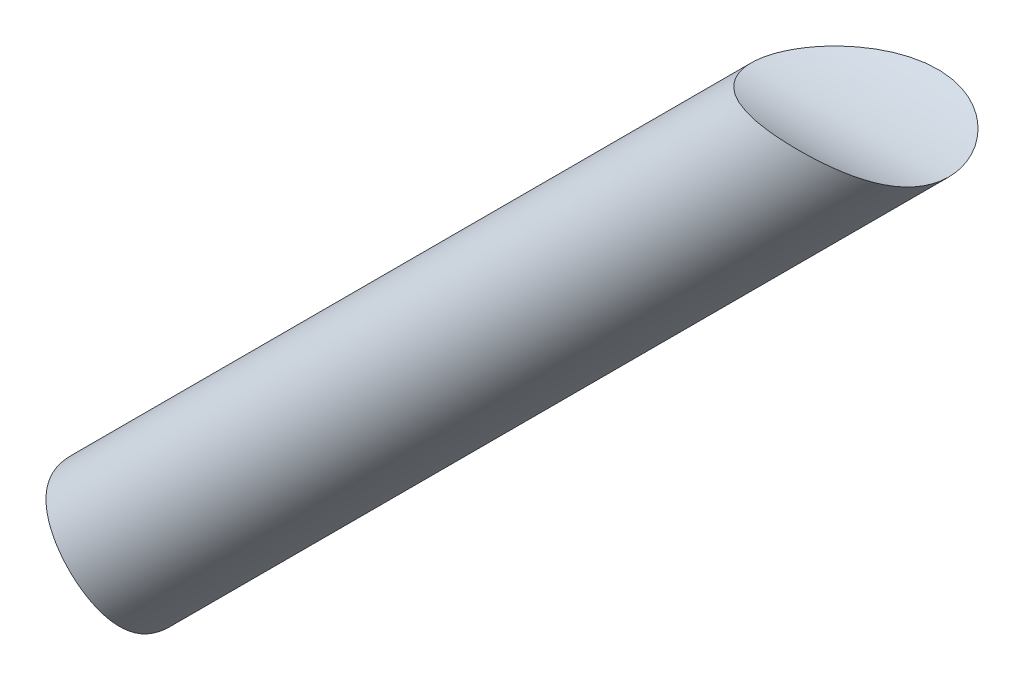
SolidWorks part; units mm, degrees
ref_plane "Front Plane" through (0, 0, 0) normal (0, 0, 1) x (1, 0, 0)
ref_plane "Top Plane" through (0, 0, 0) normal (0, 1, 0) x (1, 0, 0)
ref_plane "Right Plane" through (0, 0, 0) normal (1, 0, 0) x (0, 0, -1)
sketch "Sketch1" plane through (0, 0, 0) normal (0, 0, 1) x (1, 0, 0)
  line L1 (0, 0) -> (76.3087, 0)
  line L2 (0, 0) -> (0, 1.9255)
  line L3 (0, 1.9255) -> (76.3087, 1.9255)
  line L4 (76.3087, 0) -> (76.3087, 1.9255)
sketch "Sketch9" plane through (0, 0, 0) normal (0, 0, 1) x (1, 0, 0)
  circle A0 centre (0, 0) radius 8
  circle A1 centre (0, 0) radius 9
  dimension "D1" = 16
  dimension "D2" = 18
extrude "Boss-Extrude1" add sketch "Sketch9" along normal blind 20
sketch "Sketch10" plane through (0, 0, 20) normal (0, 0, 1) x (1, 0, 0)
  line L1 (10.4675, 0.1) -> (5.5325, 0.1)
  line L2 (10.4675, 0.1) -> (10.4675, -0.1)
  line L3 (10.4675, -0.1) -> (5.5325, -0.1)
  line L4 (5.5325, 0.1) -> (5.5325, -0.1)
  line L5 (10.4675, 0.1) -> (5.5325, -0.1) construction
  line L6 (10.4675, -0.1) -> (5.5325, 0.1) construction
  circle A0 centre (0, 0) radius 8 construction
  point P0 (8, 0)
  dimension "D1" = 0.2
extrude "Cut-Extrude1" cut sketch "Sketch10" against normal blind 20
ref_plane "Plane1" through (-6.364, 6.364, 0) normal (-0.7071, 0.7071, 0) x (0, 0, -1)
sketch "Sketch11" plane through (-6.364, 6.364, 0) normal (-0.7071, 0.7071, 0) x (0, 0, -1)
  line L0 (0, -9) -> (0, 9) construction
  circle A0 centre (-10, 0) radius 6
  dimension "D1" = 12
  dimension "D2" = 10
extrude "Boss-Extrude2" add sketch "Sketch11" along normal blind 100 and the other way up to surface
ref_plane "Plane2" through (6.364, 6.364, 0) normal (0.7071, 0.7071, 0) x (0, 0, -1)
sketch "Sketch12" plane through (6.364, 6.364, 0) normal (0.7071, 0.7071, 0) x (0, 0, -1)
  line L0 (0, -9) -> (0, 9) construction
  circle A0 centre (-10, 0) radius 6
  dimension "D1" = 12
  dimension "D2" = 10
extrude "Boss-Extrude3" add sketch "Sketch12" along normal blind 100 and the other way up to surface
sketch "Sketch14" plane through (0, 0, 0) normal (1, 0, 0) x (0, 0, -1)
  circle A0 centre (-10, 79.9) radius 12.5
  dimension "D1" = 25
  dimension "D2" = 80
extrude "Cut-Extrude3" cut sketch "Sketch14" against normal through all and the other way through all
sketch "Sketch15" plane through (0, 0, 20) normal (0, 0, 1) x (1, 0, 0)
  line L1 (-9, 0) -> (-109.9791, 0)
  line L2 (0, 9) -> (0, 78.9238)
  line L3 (0, 78.9238) -> (-109.9791, 78.9238)
  line L4 (-109.9791, 0) -> (-109.9791, 78.9238)
  arc A0 (-9, 0) -> (0, 9) centre (0, 0) ccw
extrude "Cut-Extrude4" cut sketch "Sketch15" against normal through all
sketch "Bend-Lines1" [suppressed] plane through (0, 0, 0) normal (0, 1, 0) x (1, 0, 0)
sketch "Bounding-Box1" [suppressed] plane through (0, 0, 0) normal (0, 1, 0) x (1, 0, 0)
